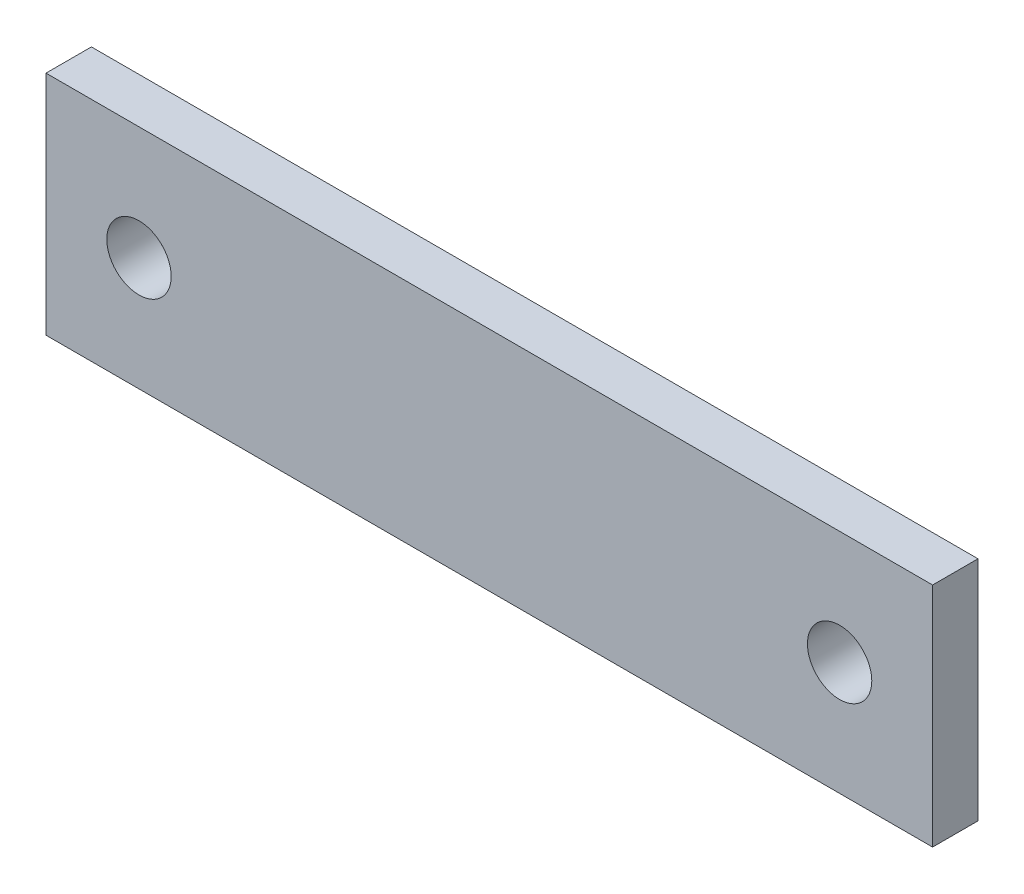
SolidWorks part; units mm, degrees
material "6061 Alloy"
ref_plane "Front Plane" through (0, 0, 0) normal (0, 0, 1) x (1, 0, 0)
ref_plane "Top Plane" through (0, 0, 0) normal (0, 1, 0) x (1, 0, 0)
ref_plane "Right Plane" through (0, 0, 0) normal (1, 0, 0) x (0, 0, -1)
sketch "Sketch2" plane through (0, 0, 0) normal (0, 0, 1) x (1, 0, 0)
  line L1 (-30.5785, 16.9368) -> (31.4229, 16.9368)
  line L2 (-30.5785, 16.9368) -> (-30.5785, 1.0618)
  line L3 (-30.5785, 1.0618) -> (31.4229, 1.0618)
  line L4 (31.4229, 16.9368) -> (31.4229, 1.0618)
  dimension "D1" = 62.0014
  dimension "D2" = 15.875
extrude "Boss-Extrude1" add sketch "Sketch2" along normal blind 3.175
hole_wizard "M4 Clearance Hole1" positions "Sketch4" profile "Sketch3" hole size "M4" standard "ANSI Metric" end condition through all
sketch "Sketch4" plane through (0, 0, 3.175) normal (0, 0, 1) x (1, 0, 0)
  line L0 (-30.5785, 16.9368) -> (-30.5785, 1.0618) construction
  line L1 (31.4229, 16.9368) -> (-30.5785, 16.9368) construction
  point P0 (-24.0761, 8.9993)
  point P2 (24.9205, 8.9993)
  dimension "D1" = 48.9966
  dimension "D2" = 6.5024
  dimension "D3" = 7.9375
  dimension "D4" = 7.9375
sketch "Sketch3" plane through (-24.0761, 8.9993, 3.175) normal (1, 0, 0) x (0, -1, 0)
  line L0 (0, 0) -> (0, 3.175)
  line L1 (0, 3.175) -> (2.25, 3.175)
  line L2 (2.25, 3.175) -> (2.25, 0)
  line L5 (2.25, 0) -> (0, 0)
  line L11 (0, -6.35) -> (0, 107.95) construction
  dimension "Thru Hole Dia." = 4.5
  dimension "Thru Hole Depth" = 3.175
